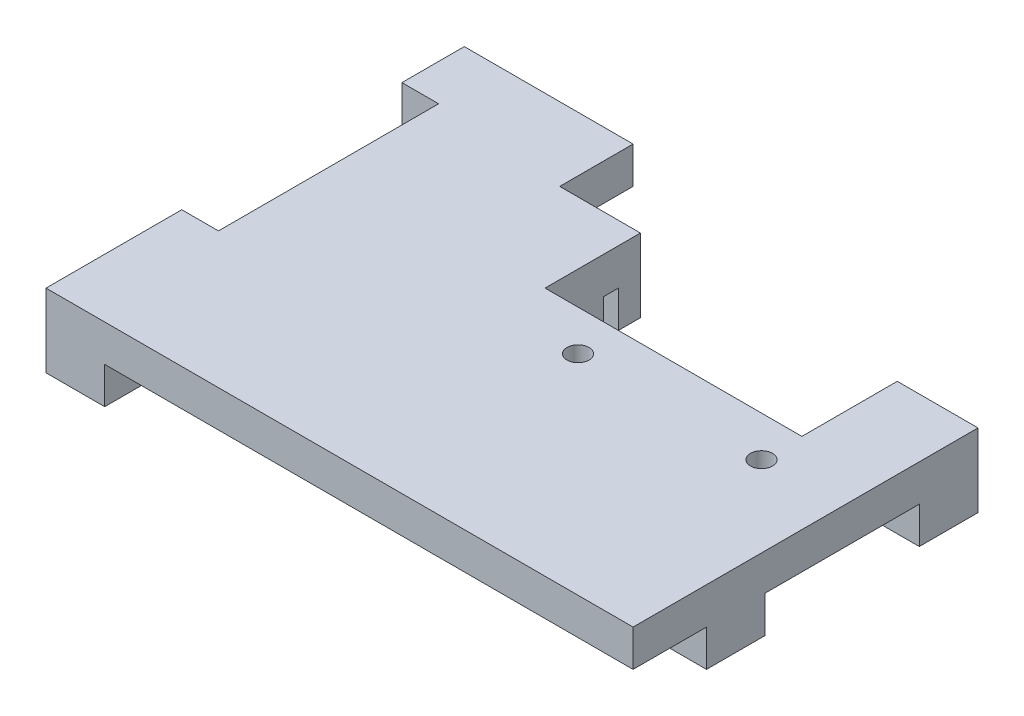
SolidWorks part; units mm, degrees
ref_plane "Front Plane" through (0, 0, 0) normal (0, 0, 1) x (1, 0, 0)
ref_plane "Top Plane" through (0, 0, 0) normal (0, 1, 0) x (1, 0, 0)
ref_plane "Right Plane" through (0, 0, 0) normal (1, 0, 0) x (0, 0, -1)
sketch "Sketch1" plane through (0, 0, 0) normal (0, 1, 0) x (1, 0, 0)
  line L0 (-4, -28.5) -> (-4, 28.5)
  line L1 (-1, -25.5) -> (1, -25.5)
  line L2 (-1, -25.5) -> (-1, 25.5)
  line L3 (-1, 25.5) -> (1, 25.5)
  line L4 (1, -25.5) -> (1, 25.5)
  line L5 (-1, -25.5) -> (1, 25.5) construction
  line L6 (-1, 25.5) -> (1, -25.5) construction
  line L7 (-4, 28.5) -> (4, 28.5)
  line L8 (4, -28.5) -> (4, 28.5)
  line L9 (-4, -28.5) -> (4, -28.5)
  point P0 (0, 0)
  dimension "D1" = 2
  dimension "D2" = 51
  dimension "D3" = 3
extrude "Boss-Extrude1" add sketch "Sketch1" along normal blind 5
sketch "Sketch2" plane through (0, 5, 0) normal (0, 1, 0) x (1, 0, 0)
  line L0 (-4, -28.5) -> (4, -28.5) construction
  line L1 (-4, 28.5) -> (76, 28.5)
  line L2 (-4, 28.5) -> (-4, -28.5)
  line L3 (-4, -28.5) -> (76, -28.5)
  line L4 (76, 28.5) -> (76, -28.5)
  dimension "D1" = 80
extrude "Boss-Extrude2" add sketch "Sketch2" along normal blind 5
sketch "Sketch3" plane through (-4, 0, 0) normal (-1, 0, 0) x (0, 0, 1)
  line L1 (-20, -5) -> (20, -5)
  line L2 (-20, -5) -> (-20, 5)
  line L3 (-20, 5) -> (20, 5)
  line L4 (20, -5) -> (20, 5)
  line L5 (-20, -5) -> (20, 5) construction
  line L6 (-20, 5) -> (20, -5) construction
  point P0 (0, 0)
  dimension "D1" = 40
extrude "Cut-Extrude1" cut sketch "Sketch3" against normal up to surface (8 mm away) up to face at (4, 2.5, 0)
sketch "Sketch4" plane through (0, 5, 0) normal (0, -1, 0) x (1, 0, 0)
  line L1 (73, 15.5) -> (22, 15.5)
  line L2 (73, 15.5) -> (73, 13.5)
  line L3 (73, 13.5) -> (22, 13.5)
  line L4 (22, 15.5) -> (22, 13.5)
  line L5 (76, 18.5) -> (19, 18.5)
  line L6 (19, 18.5) -> (19, 10.5)
  line L7 (76, 10.5) -> (19, 10.5)
  line L8 (76, 18.5) -> (76, 10.5)
  line L9 (76, 28.5) -> (76, -28.5) construction
  line L10 (4, 28.5) -> (76, 28.5) construction
  dimension "D1" = 51
  dimension "D3" = 2
  dimension "D4" = 10
  dimension "D2" = 3
extrude "Boss-Extrude3" add sketch "Sketch4" along normal blind 5
sketch "Sketch5" plane through (0, 0, 18.5) normal (0, 0, 1) x (1, 0, 0)
  line L0 (76, 0) -> (19, 0) construction
  line L1 (30, -5) -> (65, -5)
  line L2 (30, -5) -> (30, 5)
  line L3 (30, 5) -> (65, 5)
  line L4 (65, -5) -> (65, 5)
  line L5 (30, -5) -> (65, 5) construction
  line L6 (30, 5) -> (65, -5) construction
  line L7 (4, 5) -> (76, 5) construction
  point P0 (47.5, 0)
  dimension "D1" = 35
extrude "Cut-Extrude2" cut sketch "Sketch5" against normal up to surface (8 mm away) up to face at (47.5, 2.5, 10.5)
mirror "Mirror2" about plane through (0, 0, 0) normal (0, 0, 1) of "Cut-Extrude2", "Boss-Extrude3"
sketch "Sketch6" plane through (0, 5, 0) normal (0, -1, 0) x (1, 0, 0)
  line L1 (76, -28.5) -> (19, -28.5)
  line L2 (76, -28.5) -> (76, -18.5)
  line L3 (76, -18.5) -> (19, -18.5)
  line L4 (19, -28.5) -> (19, -18.5)
  line L5 (65, -10.5) -> (30, -10.5)
  line L6 (65, -10.5) -> (65, -18.5)
  line L7 (65, -18.5) -> (30, -18.5)
  line L8 (30, -10.5) -> (30, -18.5)
  line L9 (30, -10.5) -> (65, -10.5)
  line L10 (30, -10.5) -> (30, -5.5)
  line L11 (30, -5.5) -> (65, -5.5)
  line L12 (65, -10.5) -> (65, -5.5)
  line M1 (65, -13.5) -> (65, -10.5)
  line M26 (4, -28.5) -> (76, -28.5)
  line M27 (76, -28.5) -> (76, -18.5)
  line M28 (76, -18.5) -> (65, -18.5)
  line M29 (65, -18.5) -> (65, -15.5)
  line M43 (30, -10.5) -> (30, -13.5)
  line M47 (30, -15.5) -> (30, -18.5)
  line M48 (30, -18.5) -> (19, -18.5)
  dimension "D1" = 5
extrude "Cut-Extrude3" cut sketch "Sketch6" against normal through all both and the other way through all contours L8 L3 L6 L5 M43 M47 M29 M1 | L4 L3 M26 M27 M28 M48 | L5 L12 L11 L10
sketch "Sketch7" plane through (-4, 0, 0) normal (-1, 0, 0) x (0, 0, 1)
  line L1 (-28.5, 10) -> (28.5, 10) construction
  line L2 (-20, 5) -> (10, 5)
  line L3 (-20, 5) -> (-20, 10)
  line L4 (-20, 10) -> (10, 10)
  line L6 (10, 5) -> (10, 10)
  dimension "D1" = 30
extrude "Cut-Extrude5" cut sketch "Sketch7" against normal up to surface (5 mm away) up to face at (1, 2.5, 22.75)
sketch "Sketch8" plane through (0, 10, 0) normal (0, 1, 0) x (1, 0, 0)
  line L3 (1, 0) -> (76, 0) construction
  line L4 (76, -28.5) -> (76, 18.5) construction
  line L5 (1, 20) -> (1, -10) construction
  circle A0 centre (65, 0) radius 1.5
  circle A1 centre (40, 0) radius 1.5
  dimension "D1" = 3
  dimension "D2" = 3
  dimension "D3" = 25
extrude "Cut-Extrude6" cut sketch "Sketch8" against normal through all both and the other way through all
